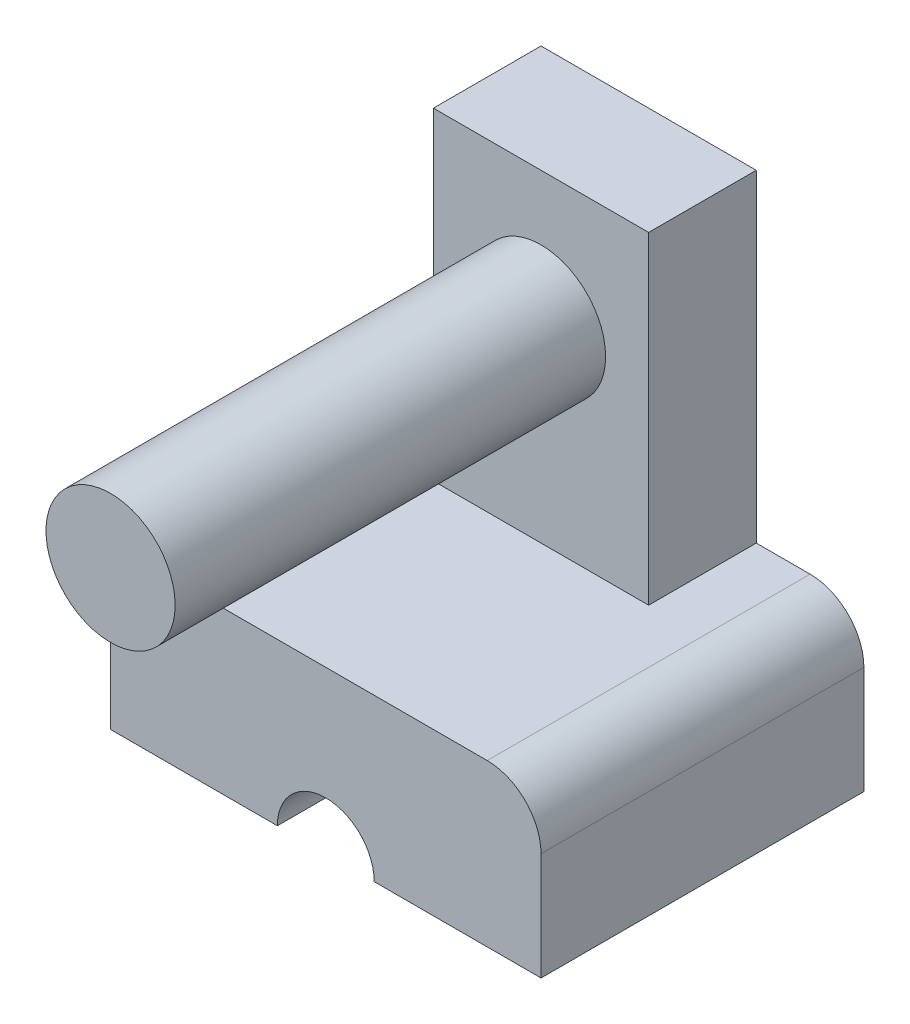
SolidWorks part; units mm, degrees
material "ABS"
ref_plane "Plan de face" through (0, 0, 0) normal (0, 0, 1) x (1, 0, 0)
ref_plane "Plan de dessus" through (0, 0, 0) normal (0, 1, 0) x (1, 0, 0)
ref_plane "Plan de droite" through (0, 0, 0) normal (1, 0, 0) x (0, 0, -1)
sketch "Esquisse1" plane through (0, 0, 0) normal (0, 0, 1) x (1, 0, 0)
  line L1 (0, 0) -> (-20, 0)
  line L2 (0, 0) -> (0, 30)
  line L3 (0, 30) -> (-20, 30)
  line L4 (-20, 0) -> (-20, 30)
  dimension "D1" = 20
  dimension "D2" = 30
extrude "Boss.-Extru.1" add sketch "Esquisse1" along normal blind 10
sketch "Esquisse2" plane through (0, 0, 10) normal (0, 0, 1) x (1, 0, 0)
  line L0 (-10, 0) -> (-10, 30) construction
  line L1 (-20, 0) -> (0, 0) construction
  line L2 (0, 30) -> (-20, 30) construction
  line L3 (-20, 0) -> (-20, 18) construction
  line L4 (-20, 30) -> (-20, 0) construction
  line L5 (-20, 18) -> (0, 18) construction
  line L6 (0, 0) -> (0, 30) construction
  circle A0 centre (-10, 18) radius 6
  dimension "D2" = 12
  dimension "D1" = 18
extrude "Boss.-Extru.2" add sketch "Esquisse2" along normal blind 40
sketch "Esquisse3" plane through (0, 0, 0) normal (0, -1, 0) x (1, 0, 0)
  line L0 (-10, 0) -> (10, 0) construction
  line L1 (-20, 0) -> (0, 0) construction
  line L2 (-10, 0) -> (-30, 0) construction
  line L4 (10, 0) -> (-30, 0)
  line L5 (10, 0) -> (10, 30)
  line L6 (10, 30) -> (-30, 30)
  line L7 (-30, 0) -> (-30, 30)
  dimension "D1" = 20
  dimension "D2" = 20
  dimension "D3" = 30
extrude "Boss.-Extru.3" add sketch "Esquisse3" along normal blind 15
sketch "Esquisse4" plane through (0, 0, 0) normal (0, 0, -1) x (-1, 0, 0)
  line L0 (30, -15) -> (-10, -15) construction
  circle A0 centre (10, -15) radius 4.5
  dimension "D1" = 9
extrude "Enlèv. mat.-Extru.1" cut sketch "Esquisse4" against normal blind 55
sketch "Esquisse5" plane through (0, 0, 0) normal (0, 0, -1) x (-1, 0, 0)
  line L0 (-2.25, -15) -> (-5, -15)
  line L1 (5.5, -15) -> (-10, -15) construction
  line L2 (-10, -10) -> (-10, -5)
  line L3 (-5, 0) -> (25, 0)
  line L4 (30, -5) -> (30, -10)
  line L5 (25, -15) -> (20.9044, -15)
  line L6 (30, -15) -> (14.5, -15) construction
  line L7 (-2.25, -15) -> (-10, -15)
  line L8 (-10, -15) -> (-10, 0)
  line L9 (-10, 0) -> (30, 0)
  line L10 (30, 0) -> (30, -15)
  line L11 (30, -15) -> (20.9044, -15)
  arc A0 (25, -15) -> (30, -10) centre (25, -10) ccw
  arc A1 (30, -5) -> (25, 0) centre (25, -5) ccw
  arc A2 (-5, -15) -> (-10, -10) centre (-5, -10) cw
  arc A3 (-10, -5) -> (-5, 0) centre (-5, -5) cw
  point P16 (30, -15)
  point P19 (30, 0)
  point P22 (-10, -15)
  point P25 (-10, 0)
  line M18 (30, -15) -> (30, 0)
  line M19 (30, 0) -> (20, 0)
  line M23 (0, 0) -> (-10, 0)
  line M24 (-10, 0) -> (-10, -15)
  dimension "D1" = 5
extrude "Enlèv. mat.-Extru.3" cut sketch "Esquisse5" against normal blind 55 contours A1 M18 M19 | A3 M24 M23
